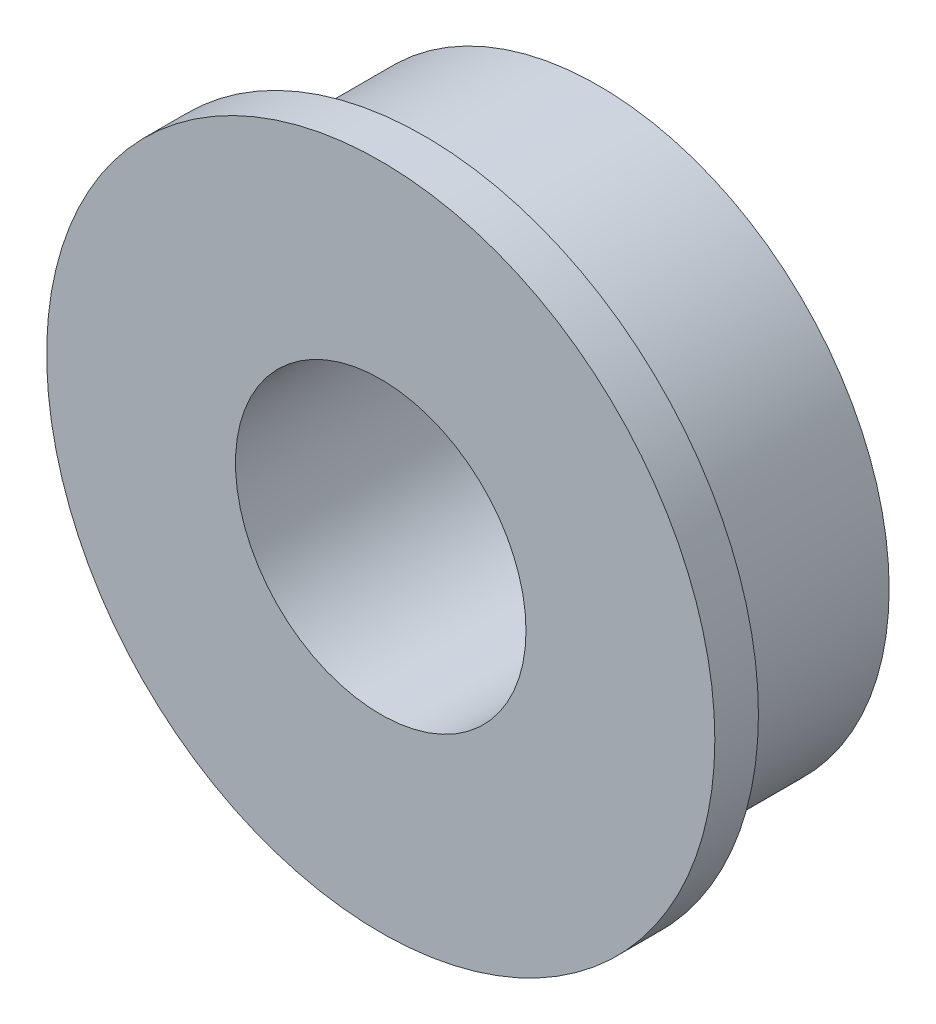
SolidWorks part; units mm, degrees
ref_plane "Front Plane" through (0, 0, 0) normal (0, 0, 1) x (1, 0, 0)
ref_plane "Top Plane" through (0, 0, 0) normal (0, 1, 0) x (1, 0, 0)
ref_plane "Right Plane" through (0, 0, 0) normal (1, 0, 0) x (0, 0, -1)
sketch "Sketch1" plane through (0, 0, 0) normal (0, 0, 1) x (1, 0, 0)
  circle A0 centre (0, 0) radius 2
  circle A1 centre (0, 0) radius 4
  dimension "D1" = 4
  dimension "D2" = 8
extrude "Boss-Extrude1" add sketch "Sketch1" against normal blind 3
sketch "Sketch2" plane through (0, 0, 0) normal (0, 0, 1) x (1, 0, 0)
  circle A0 centre (0, 0) radius 4.6
  circle M1 centre (0, 0) radius 2
  circle M2 centre (0, 0) radius 4
  dimension "D1" = 9.2
extrude "Boss-Extrude2" add sketch "Sketch2" against normal blind 0.6 contours M2 M1 | A0 M2
